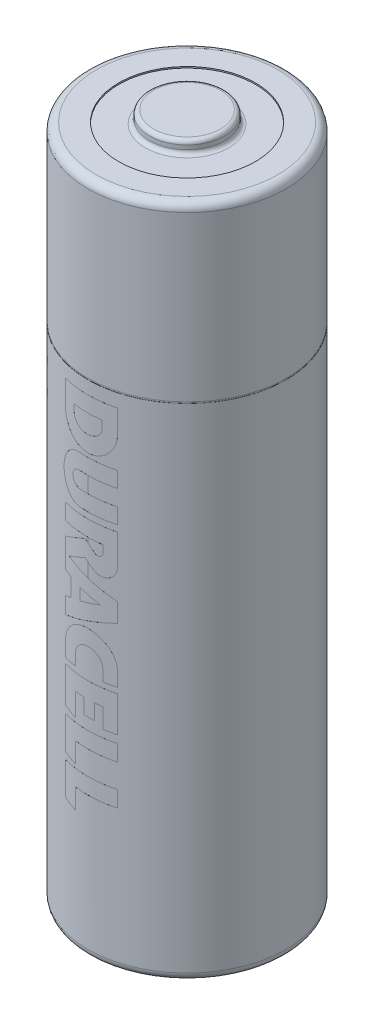
SolidWorks part; units mm, degrees
ref_plane "Front Plane" through (0, 0, 0) normal (0, 0, 1) x (1, 0, 0)
ref_plane "Top Plane" through (0, 0, 0) normal (0, 1, 0) x (1, 0, 0)
ref_plane "Right Plane" through (0, 0, 0) normal (1, 0, 0) x (0, 0, -1)
sketch "Sketch1" plane through (0, 0, 0) normal (0, 0, 1) x (1, 0, 0)
  line L0 (0, 0) -> (0, -50.5)
  line L1 (0, -55) -> (0, 55) construction
  line L2 (0, 0) -> (2.45, 0)
  line L3 (55, 0) -> (-55, 0) construction
  line L4 (2.75, -0.3) -> (2.75, -0.6)
  line L5 (3.05, -0.9) -> (5, -0.9)
  line L6 (7.25, -1.4) -> (7.25, -13.4)
  line L7 (6.65, -50.2) -> (5, -50.2)
  line L8 (5, -50.2) -> (5, -50.1)
  line L9 (5, -50.1) -> (3.6036, -50.1)
  line L10 (3.4536, -50.1402) -> (2.9, -50.4598)
  line L11 (2.75, -50.5) -> (0, -50.5)
  line L12 (7.25, -13.5) -> (7.25, -49.6)
  line L13 (5, -0.9) -> (5, -0.8)
  line L14 (5, -0.8) -> (6.65, -0.8)
  line L15 (7.25, -13.4) -> (7.24, -13.4)
  line L17 (7.25, -13.5) -> (7.24, -13.5)
  line L18 (7.24, -13.4) -> (7.24, -13.5)
  arc A0 (2.75, -0.6) -> (3.05, -0.9) centre (3.05, -0.6) ccw
  arc A1 (2.45, 0) -> (2.75, -0.3) centre (2.45, -0.3) cw
  arc A2 (7.25, -49.6) -> (6.65, -50.2) centre (6.65, -49.6) cw
  arc A3 (6.65, -0.8) -> (7.25, -1.4) centre (6.65, -1.4) cw
  arc A4 (3.6036, -50.1) -> (3.4536, -50.1402) centre (3.6036, -50.4) ccw
  arc A5 (2.9, -50.4598) -> (2.75, -50.5) centre (2.75, -50.2) cw
  point P21 (2.75, 0)
  point P28 (3.5232, -50.1)
  dimension "D10" = 0.3
  dimension "D11" = 0.6
  dimension "D12" = 0.3
  dimension "D1" = 50.5
  dimension "D2" = 7.25
  dimension "D3" = 0.9
  dimension "D4" = 2.75
  dimension "D5" = 0.1
  dimension "D6" = 0.4
  dimension "D7" = 5
  dimension "D8" = 30
  dimension "D9" = 2.75
  dimension "D13" = 0.1
  dimension "D14" = 0.01
  dimension "D15" = 12.5
revolve "Revolve1" add sketch "Sketch1" angle 360 about L0
sketch "Sketch3" plane through (0, 0, 0) normal (0, 0, 1) x (1, 0, 0)
  line L0 (0.5204, -24.271) -> (-0.2142, -23.661)
  line L1 (-0.2142, -23.661) -> (-1.9044, -24.4732)
  line L2 (-1.9044, -24.4732) -> (-1.9044, -26.5841)
  line L3 (-1.9044, -26.5841) -> (-1.3968, -26.7286)
  line L4 (-1.3968, -26.7286) -> (-1.3968, -28.0706)
  line L5 (-1.3968, -28.0706) -> (-1.9044, -28.2283)
  line L6 (-1.9044, -28.2283) -> (-1.9044, -29.452)
  line L7 (-1.9044, -29.452) -> (1.9044, -28.1134)
  line L8 (1.9044, -28.1134) -> (1.9044, -26.7307)
  line L9 (1.9044, -26.7307) -> (-1.5551, -25.515)
  line L10 (-1.5551, -25.515) -> (-0.2053, -24.8663)
  line L11 (-0.2053, -24.8663) -> (0.3349, -25.3148)
  line L12 (1.9044, -24.578) -> (1.9044, -22.3266)
  line L13 (1.9044, -22.3266) -> (-1.9044, -22.3266)
  line L14 (-1.9044, -22.3266) -> (-1.9044, -23.4783)
  line L15 (-1.9044, -23.4783) -> (1.016, -23.4783)
  line L16 (0.8562, -27.3703) -> (-0.6269, -26.9479)
  line L17 (-0.6269, -26.9479) -> (-0.6269, -27.8313)
  line L18 (-0.6269, -27.8313) -> (0.8562, -27.3703)
  line L19 (0.9731, -16.1256) -> (0.9731, -15.6129)
  line L20 (0.9731, -15.6129) -> (-1.0911, -15.6129)
  line L21 (-1.0911, -15.6129) -> (-1.0911, -16.1256)
  line L22 (-1.9044, -16.1868) -> (-1.9044, -14.4608)
  line L23 (-1.9044, -14.4608) -> (1.9044, -14.4608)
  line L24 (1.9044, -14.4608) -> (1.9044, -16.1868)
  line L25 (-0.6242, -18.4154) -> (1.9044, -18.4154)
  line L26 (1.9044, -18.4154) -> (1.9044, -19.5605)
  line L27 (1.9044, -19.5605) -> (-0.6242, -19.5605)
  line L28 (-0.6242, -20.7251) -> (1.9044, -20.7251)
  line L29 (1.9044, -20.7251) -> (1.9044, -21.8703)
  line L30 (1.9044, -21.8703) -> (-0.6242, -21.8703)
  line L31 (-0.3024, -33.7493) -> (-0.984, -33.7493)
  line L32 (-0.984, -33.7493) -> (-0.984, -35.4377)
  line L33 (-0.984, -35.4377) -> (-1.9044, -35.175)
  line L34 (-1.9044, -35.175) -> (-1.9044, -32.5726)
  line L35 (-1.9044, -32.5726) -> (1.9044, -32.5726)
  line L36 (1.9044, -32.5726) -> (1.9044, -35.1774)
  line L37 (1.9044, -35.1774) -> (1.0183, -35.1774)
  line L38 (1.0183, -35.1774) -> (1.0183, -33.7493)
  line L39 (1.0183, -33.7493) -> (0.473, -33.7493)
  line L40 (0.473, -33.7493) -> (0.473, -34.879)
  line L41 (0.473, -34.879) -> (-0.3024, -34.879)
  line L42 (-0.3024, -34.879) -> (-0.3024, -33.7493)
  line L43 (-1.9044, -35.7276) -> (1.9044, -35.7276)
  line L44 (1.9044, -35.7276) -> (1.9044, -36.9043)
  line L45 (1.9044, -36.9043) -> (-0.984, -36.9043)
  line L46 (-0.984, -36.9043) -> (-0.984, -38.3795)
  line L47 (-0.984, -38.3795) -> (-1.9044, -38.1168)
  line L48 (-1.9044, -38.1168) -> (-1.9044, -35.7276)
  line L49 (1.9044, -32.1649) -> (1.9044, -30.9947)
  line L50 (-1.9044, -30.9947) -> (-1.9044, -32.1649)
  line L51 (-1.9044, -32.1649) -> (-0.984, -32.1649)
  line L52 (-0.984, -32.1649) -> (-0.984, -31.2931)
  line L53 (1.0183, -31.2931) -> (1.0183, -32.1649)
  line L54 (1.0183, -32.1649) -> (1.9044, -32.1649)
  line L55 (-1.9044, -38.6438) -> (1.9044, -38.6438)
  line L56 (1.9044, -38.6438) -> (1.9044, -39.8205)
  line L57 (1.9044, -39.8205) -> (-0.984, -39.8205)
  line L58 (-0.984, -39.8205) -> (-0.984, -41.2957)
  line L59 (-0.984, -41.2957) -> (-1.9044, -41.033)
  line L60 (-1.9044, -41.033) -> (-1.9044, -38.6438)
  line L61 (1.016, -23.4783) -> (1.016, -24.0383)
  arc A0 (0.5204, -24.271) -> (1.016, -24.0383) centre (0.7136, -24.0383) ccw
  arc A1 (0.3349, -25.3148) -> (1.9044, -24.578) centre (0.9467, -24.578) ccw
  arc A2 (-0.6242, -19.5605) -> (-0.6242, -20.7251) centre (-0.6242, -20.1428) ccw
  arc A3 (1.9044, -30.9947) -> (-1.9044, -30.9947) centre (0, -31.1628) ccw
  arc A4 (1.0183, -31.2931) -> (-0.984, -31.2931) centre (0.0171, -31.3964) ccw
  ellipse E0 centre (-0.059, -16.1256) end of major axis (-1.0911, -16.1256) minor radius 0.8416 (-1.0911, -16.1256) -> (0.9731, -16.1256) ccw
  ellipse E1 centre (0, -16.1868) end of major axis (0, -18.1378) minor radius 1.9044 (-1.9044, -16.1868) -> (1.9044, -16.1868) ccw
  ellipse E2 centre (-0.6242, -20.1428) end of major axis (-0.6242, -21.8703) minor radius 1.4146 (-0.6242, -18.4154) -> (-0.6242, -21.8703) ccw
extrude "Boss-Extrude1" add sketch "Sketch3" along normal offset from surface (7.2323 mm away) 0.001
sketch "Sketch5" plane through (0, 0, 0) normal (0, 1, 0) x (1, 0, 0)
  line L0 (0, 0) -> (-5.0548, -4.005) construction
ref_plane "Plane1" through (-5.0548, 0, 4.005) normal (-0.7838, 0, 0.621) x (0.621, 0, 0.7838)
sketch "Sketch6" plane through (-5.0548, 0, 4.005) normal (-0.7838, 0, 0.621) x (0.621, 0, 0.7838)
  line L0 (-0.8313, -14.6983) -> (-0.8313, -40.6859) construction
  text T0 "AA" font "Humnst777 BT" height 2.4
extrude "Boss-Extrude2" add sketch "Sketch6" along normal offset from surface (0.8012 mm away) 0.001
